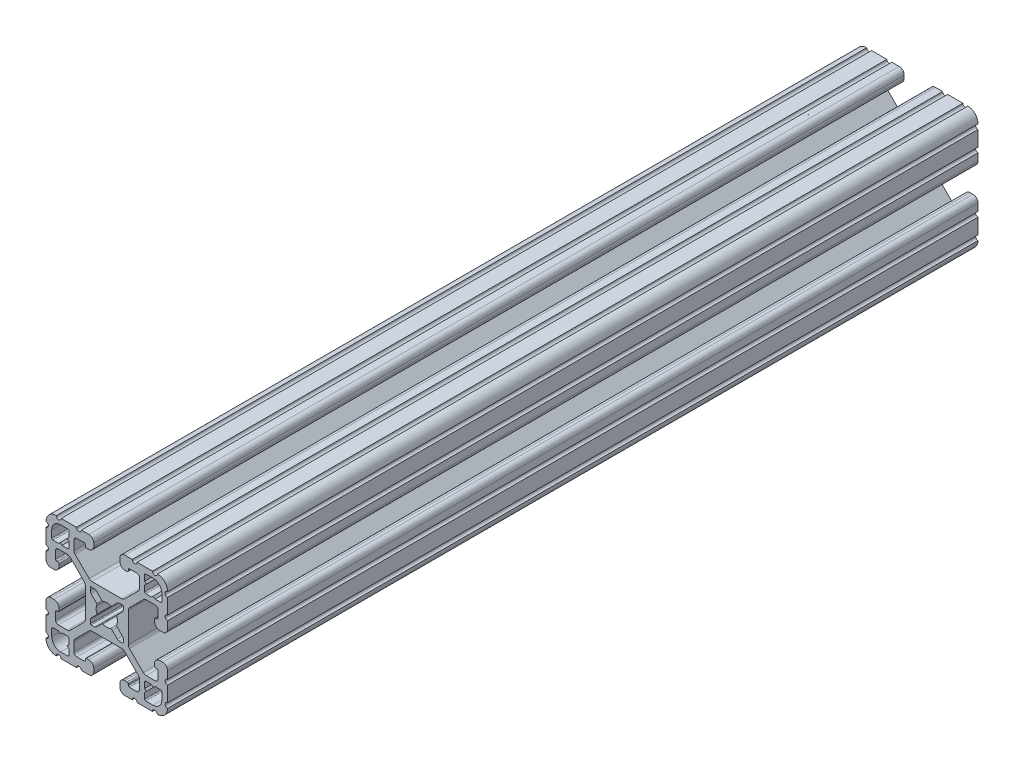
SolidWorks part; units mm, degrees
ref_plane "Front Plane" through (0, 0, 0) normal (0, 0, 1) x (1, 0, 0)
ref_plane "Top Plane" through (0, 0, 0) normal (0, 1, 0) x (1, 0, 0)
ref_plane "Right Plane" through (0, 0, 0) normal (1, 0, 0) x (0, 0, -1)
sketch "Sketch1" plane through (0, 0, 0) normal (0, 0, 1) x (1, 0, 0)
  line L0 (1.5823, 3.1988) -> (3.2921, 4.9085)
  line L1 (3.9207, 5.1689) -> (4.9149, 5.1689)
  line L2 (5.1689, 4.9149) -> (5.1689, 3.9207)
  line L3 (4.9085, 3.2921) -> (3.1988, 1.5823)
  line L4 (3.1988, -1.5823) -> (4.9085, -3.2921)
  line L5 (5.1689, -3.9207) -> (5.1689, -4.9149)
  line L6 (4.9149, -5.1689) -> (3.9207, -5.1689)
  line L7 (3.2921, -4.9085) -> (1.5823, -3.1988)
  line L8 (-1.5823, -3.1988) -> (-3.2921, -4.9085)
  line L9 (-3.9207, -5.1689) -> (-4.9149, -5.1689)
  line L10 (-5.1689, -4.9149) -> (-5.1689, -3.9207)
  line L11 (-4.9085, -3.2921) -> (-3.1988, -1.5823)
  line L12 (-3.1988, 1.5823) -> (-4.9085, 3.2921)
  line L13 (-5.1689, 3.9207) -> (-5.1689, 4.9149)
  line L14 (-4.9149, 5.1689) -> (-3.9207, 5.1689)
  line L15 (-3.2921, 4.9085) -> (-1.5823, 3.1988)
  line L16 (-11.8669, 14.0194) -> (-11.8669, 12.2479)
  line L17 (-12.2479, 11.8669) -> (-14.0195, 11.8669)
  line L18 (-14.0213, 11.8676) -> (-14.5575, 12.4039)
  line L19 (-14.5611, 12.4039) -> (-15.0973, 11.8676)
  line L20 (-15.0991, 11.8669) -> (-16.8707, 11.8669)
  line L21 (-17.2517, 12.2479) -> (-17.2517, 14.4577)
  line L22 (-14.4577, 17.2517) -> (-12.2479, 17.2517)
  line L23 (-11.8669, 16.8707) -> (-11.8669, 15.0991)
  line L24 (-11.8676, 15.0973) -> (-12.4039, 14.5611)
  line L25 (-12.4039, 14.5575) -> (-11.8676, 14.0212)
  line L26 (-14.0194, -11.8669) -> (-12.2479, -11.8669)
  line L27 (-11.8669, -12.2479) -> (-11.8669, -14.0195)
  line L28 (-11.8676, -14.0213) -> (-12.4039, -14.5575)
  line L29 (-12.4039, -14.5611) -> (-11.8676, -15.0973)
  line L30 (-11.8669, -15.0991) -> (-11.8669, -16.8707)
  line L31 (-12.2479, -17.2517) -> (-14.4577, -17.2517)
  line L32 (-17.2517, -14.4577) -> (-17.2517, -12.2479)
  line L33 (-16.8707, -11.8669) -> (-15.0991, -11.8669)
  line L34 (-15.0973, -11.8676) -> (-14.5611, -12.4039)
  line L35 (-14.5575, -12.4039) -> (-14.0212, -11.8676)
  line L36 (11.8669, -14.0194) -> (11.8669, -12.2479)
  line L37 (12.2479, -11.8669) -> (14.0195, -11.8669)
  line L38 (14.0213, -11.8676) -> (14.5575, -12.4039)
  line L39 (14.5611, -12.4039) -> (15.0973, -11.8676)
  line L40 (15.0991, -11.8669) -> (16.8707, -11.8669)
  line L41 (17.2517, -12.2479) -> (17.2517, -14.4577)
  line L42 (14.4577, -17.2517) -> (12.2479, -17.2517)
  line L43 (11.8669, -16.8707) -> (11.8669, -15.0991)
  line L44 (11.8676, -15.0973) -> (12.4039, -14.5611)
  line L45 (12.4039, -14.5575) -> (11.8676, -14.0212)
  line L46 (14.0194, 11.8669) -> (12.2479, 11.8669)
  line L47 (11.8669, 12.2479) -> (11.8669, 14.0195)
  line L48 (11.8676, 14.0213) -> (12.4039, 14.5575)
  line L49 (12.4039, 14.5611) -> (11.8676, 15.0973)
  line L50 (11.8669, 15.0991) -> (11.8669, 16.8707)
  line L51 (12.2479, 17.2517) -> (14.4577, 17.2517)
  line L52 (17.2517, 14.4577) -> (17.2517, 12.2479)
  line L53 (16.8707, 11.8669) -> (15.0991, 11.8669)
  line L54 (15.0973, 11.8676) -> (14.5611, 12.4039)
  line L55 (14.5575, 12.4039) -> (14.0212, 11.8676)
  line L56 (6.3498, -14.9848) -> (5.6531, -14.9848)
  line L57 (4.0778, -16.5601) -> (4.0778, -17.4747)
  line L58 (5.6531, -19.05) -> (7.9756, -19.05)
  line L59 (9.4996, -19.05) -> (14.2981, -19.05)
  line L60 (19.05, -14.3256) -> (19.05, -9.4996)
  line L61 (19.05, -7.9756) -> (19.05, -5.6531)
  line L62 (17.4747, -4.0778) -> (16.5601, -4.0778)
  line L63 (14.9848, -5.6531) -> (14.9848, -6.3498)
  line L64 (15.3661, -6.731) -> (15.6969, -6.731)
  line L65 (16.0782, -7.1122) -> (16.0782, -9.3968)
  line L66 (15.1881, -10.287) -> (12.3526, -10.2871)
  line L67 (11.4535, -9.9142) -> (7.1147, -5.5659)
  line L68 (6.7437, -4.6689) -> (6.7437, 4.6414)
  line L69 (7.1147, 5.5384) -> (11.481, 9.9142)
  line L70 (12.38, 10.2871) -> (15.1881, 10.287)
  line L71 (16.0782, 9.3968) -> (16.0782, 7.1122)
  line L72 (15.6969, 6.731) -> (15.3661, 6.731)
  line L73 (14.9848, 6.3498) -> (14.9848, 5.6531)
  line L74 (16.5601, 4.0778) -> (17.4747, 4.0778)
  line L75 (19.05, 5.6531) -> (19.05, 7.9756)
  line L76 (19.05, 9.4996) -> (19.05, 14.2981)
  line L77 (14.3256, 19.05) -> (9.4996, 19.05)
  line L78 (7.9756, 19.05) -> (5.6531, 19.05)
  line L79 (4.0778, 17.4747) -> (4.0778, 16.5601)
  line L80 (5.6531, 14.9848) -> (6.3498, 14.9848)
  line L81 (6.731, 15.3661) -> (6.731, 15.6969)
  line L82 (7.1122, 16.0782) -> (9.3968, 16.0782)
  line L83 (10.287, 15.1881) -> (10.2871, 12.3526)
  line L84 (9.9142, 11.4535) -> (5.5659, 7.1147)
  line L85 (4.6689, 6.7437) -> (-4.6414, 6.7437)
  line L86 (-5.5384, 7.1147) -> (-9.9142, 11.481)
  line L87 (-10.2871, 12.38) -> (-10.287, 15.1881)
  line L88 (-9.3968, 16.0782) -> (-7.1122, 16.0782)
  line L89 (-6.731, 15.6969) -> (-6.731, 15.3661)
  line L90 (-6.3498, 14.9848) -> (-5.6531, 14.9848)
  line L91 (-4.0778, 16.5601) -> (-4.0778, 17.4747)
  line L92 (-5.6531, 19.05) -> (-7.9756, 19.05)
  line L93 (-9.4996, 19.05) -> (-14.2981, 19.05)
  line L94 (-19.05, 14.3256) -> (-19.05, 9.4996)
  line L95 (-19.05, 7.9756) -> (-19.05, 5.6531)
  line L96 (-17.4747, 4.0778) -> (-16.5601, 4.0778)
  line L97 (-14.9848, 5.6531) -> (-14.9848, 6.3498)
  line L98 (-15.3661, 6.731) -> (-15.6969, 6.731)
  line L99 (-16.0782, 7.1122) -> (-16.0782, 9.3968)
  line L100 (-15.1881, 10.287) -> (-12.3526, 10.2871)
  line L101 (-11.4535, 9.9142) -> (-7.1147, 5.5659)
  line L102 (-6.7437, 4.6689) -> (-6.7437, -4.6414)
  line L103 (-7.1147, -5.5384) -> (-11.481, -9.9142)
  line L104 (-12.38, -10.2871) -> (-15.1881, -10.287)
  line L105 (-16.0782, -9.3968) -> (-16.0782, -7.1122)
  line L106 (-15.6969, -6.731) -> (-15.3661, -6.731)
  line L107 (-14.9848, -6.3498) -> (-14.9848, -5.6531)
  line L108 (-16.5601, -4.0778) -> (-17.4747, -4.0778)
  line L109 (-19.05, -5.6531) -> (-19.05, -7.9756)
  line L110 (-19.05, -9.4996) -> (-19.05, -14.2981)
  line L111 (-14.3256, -19.05) -> (-9.4996, -19.05)
  line L112 (-7.9756, -19.05) -> (-5.6531, -19.05)
  line L113 (-4.0778, -17.4747) -> (-4.0778, -16.5601)
  line L114 (-5.6531, -14.9848) -> (-6.3498, -14.9848)
  line L115 (-6.731, -15.3661) -> (-6.731, -15.6969)
  line L116 (-7.1122, -16.0782) -> (-9.3968, -16.0782)
  line L117 (-10.287, -15.1881) -> (-10.2871, -12.3526)
  line L118 (-9.9142, -11.4535) -> (-5.5659, -7.1147)
  line L119 (-4.6689, -6.7437) -> (4.6414, -6.7437)
  line L120 (5.5384, -7.1147) -> (9.9142, -11.481)
  line L121 (10.2871, -12.38) -> (10.287, -15.1881)
  line L122 (9.3968, -16.0782) -> (7.1122, -16.0782)
  line L123 (6.731, -15.6969) -> (6.731, -15.3661)
  arc A0 (1.178, 3.1119) -> (1.5823, 3.1988) centre (1.3129, 3.4682) ccw
  arc A1 (3.9207, 5.1689) -> (3.2921, 4.9085) centre (3.9207, 4.2799) ccw
  arc A2 (5.1689, 4.9149) -> (4.9149, 5.1689) centre (4.9149, 4.9149) ccw
  arc A3 (4.9085, 3.2921) -> (5.1689, 3.9207) centre (4.2799, 3.9207) ccw
  arc A4 (3.1988, 1.5823) -> (3.1119, 1.178) centre (3.4682, 1.3129) ccw
  arc A5 (3.1119, -1.178) -> (3.1119, 1.178) centre (0, 0) ccw
  arc A6 (3.1119, -1.178) -> (3.1988, -1.5823) centre (3.4682, -1.3129) ccw
  arc A7 (5.1689, -3.9207) -> (4.9085, -3.2921) centre (4.2799, -3.9207) ccw
  arc A8 (4.9149, -5.1689) -> (5.1689, -4.9149) centre (4.9149, -4.9149) ccw
  arc A9 (3.2921, -4.9085) -> (3.9207, -5.1689) centre (3.9207, -4.2799) ccw
  arc A10 (1.5823, -3.1988) -> (1.178, -3.1119) centre (1.3129, -3.4682) ccw
  arc A11 (-1.178, -3.1119) -> (1.178, -3.1119) centre (0, 0) ccw
  arc A12 (-1.178, -3.1119) -> (-1.5823, -3.1988) centre (-1.3129, -3.4682) ccw
  arc A13 (-3.9207, -5.1689) -> (-3.2921, -4.9085) centre (-3.9207, -4.2799) ccw
  arc A14 (-5.1689, -4.9149) -> (-4.9149, -5.1689) centre (-4.9149, -4.9149) ccw
  arc A15 (-4.9085, -3.2921) -> (-5.1689, -3.9207) centre (-4.2799, -3.9207) ccw
  arc A16 (-3.1988, -1.5823) -> (-3.1119, -1.178) centre (-3.4682, -1.3129) ccw
  arc A17 (-3.1119, 1.178) -> (-3.1119, -1.178) centre (0, 0) ccw
  arc A18 (-3.1119, 1.178) -> (-3.1988, 1.5823) centre (-3.4682, 1.3129) ccw
  arc A19 (-5.1689, 3.9207) -> (-4.9085, 3.2921) centre (-4.2799, 3.9207) ccw
  arc A20 (-4.9149, 5.1689) -> (-5.1689, 4.9149) centre (-4.9149, 4.9149) ccw
  arc A21 (-3.2921, 4.9085) -> (-3.9207, 5.1689) centre (-3.9207, 4.2799) ccw
  arc A22 (-1.5823, 3.1988) -> (-1.178, 3.1119) centre (-1.3129, 3.4682) ccw
  arc A23 (1.178, 3.1119) -> (-1.178, 3.1119) centre (0, 0) ccw
  arc A24 (-11.8669, 14.0194) -> (-11.8676, 14.0212) centre (-11.8694, 14.0194) ccw
  arc A25 (-12.2479, 11.8669) -> (-11.8669, 12.2479) centre (-12.2479, 12.2479) ccw
  arc A26 (-14.0213, 11.8676) -> (-14.0195, 11.8669) centre (-14.0195, 11.8694) ccw
  arc A27 (-14.5575, 12.4039) -> (-14.5611, 12.4039) centre (-14.5593, 12.4021) ccw
  arc A28 (-15.0991, 11.8669) -> (-15.0973, 11.8676) centre (-15.0991, 11.8694) ccw
  arc A29 (-17.2517, 12.2479) -> (-16.8707, 11.8669) centre (-16.8707, 12.2479) ccw
  arc A30 (-14.4577, 17.2517) -> (-17.2517, 14.4577) centre (-14.4577, 14.4577) ccw
  arc A31 (-11.8669, 16.8707) -> (-12.2479, 17.2517) centre (-12.2479, 16.8707) ccw
  arc A32 (-11.8676, 15.0973) -> (-11.8669, 15.0991) centre (-11.8694, 15.0991) ccw
  arc A33 (-12.4039, 14.5611) -> (-12.4039, 14.5575) centre (-12.4021, 14.5593) ccw
  arc A34 (-14.0194, -11.8669) -> (-14.0212, -11.8676) centre (-14.0194, -11.8694) ccw
  arc A35 (-11.8669, -12.2479) -> (-12.2479, -11.8669) centre (-12.2479, -12.2479) ccw
  arc A36 (-11.8676, -14.0213) -> (-11.8669, -14.0195) centre (-11.8694, -14.0195) ccw
  arc A37 (-12.4039, -14.5575) -> (-12.4039, -14.5611) centre (-12.4021, -14.5593) ccw
  arc A38 (-11.8669, -15.0991) -> (-11.8676, -15.0973) centre (-11.8694, -15.0991) ccw
  arc A39 (-12.2479, -17.2517) -> (-11.8669, -16.8707) centre (-12.2479, -16.8707) ccw
  arc A40 (-17.2517, -14.4577) -> (-14.4577, -17.2517) centre (-14.4577, -14.4577) ccw
  arc A41 (-16.8707, -11.8669) -> (-17.2517, -12.2479) centre (-16.8707, -12.2479) ccw
  arc A42 (-15.0973, -11.8676) -> (-15.0991, -11.8669) centre (-15.0991, -11.8694) ccw
  arc A43 (-14.5611, -12.4039) -> (-14.5575, -12.4039) centre (-14.5593, -12.4021) ccw
  arc A44 (11.8669, -14.0194) -> (11.8676, -14.0212) centre (11.8694, -14.0194) ccw
  arc A45 (12.2479, -11.8669) -> (11.8669, -12.2479) centre (12.2479, -12.2479) ccw
  arc A46 (14.0213, -11.8676) -> (14.0195, -11.8669) centre (14.0195, -11.8694) ccw
  arc A47 (14.5575, -12.4039) -> (14.5611, -12.4039) centre (14.5593, -12.4021) ccw
  arc A48 (15.0991, -11.8669) -> (15.0973, -11.8676) centre (15.0991, -11.8694) ccw
  arc A49 (17.2517, -12.2479) -> (16.8707, -11.8669) centre (16.8707, -12.2479) ccw
  arc A50 (14.4577, -17.2517) -> (17.2517, -14.4577) centre (14.4577, -14.4577) ccw
  arc A51 (11.8669, -16.8707) -> (12.2479, -17.2517) centre (12.2479, -16.8707) ccw
  arc A52 (11.8676, -15.0973) -> (11.8669, -15.0991) centre (11.8694, -15.0991) ccw
  arc A53 (12.4039, -14.5611) -> (12.4039, -14.5575) centre (12.4021, -14.5593) ccw
  arc A54 (14.0194, 11.8669) -> (14.0212, 11.8676) centre (14.0194, 11.8694) ccw
  arc A55 (11.8669, 12.2479) -> (12.2479, 11.8669) centre (12.2479, 12.2479) ccw
  arc A56 (11.8676, 14.0213) -> (11.8669, 14.0195) centre (11.8694, 14.0195) ccw
  arc A57 (12.4039, 14.5575) -> (12.4039, 14.5611) centre (12.4021, 14.5593) ccw
  arc A58 (11.8669, 15.0991) -> (11.8676, 15.0973) centre (11.8694, 15.0991) ccw
  arc A59 (12.2479, 17.2517) -> (11.8669, 16.8707) centre (12.2479, 16.8707) ccw
  arc A60 (17.2517, 14.4577) -> (14.4577, 17.2517) centre (14.4577, 14.4577) ccw
  arc A61 (16.8707, 11.8669) -> (17.2517, 12.2479) centre (16.8707, 12.2479) ccw
  arc A62 (15.0973, 11.8676) -> (15.0991, 11.8669) centre (15.0991, 11.8694) ccw
  arc A63 (14.5611, 12.4039) -> (14.5575, 12.4039) centre (14.5593, 12.4021) ccw
  arc A64 (6.731, -15.3661) -> (6.3498, -14.9848) centre (6.35, -15.3658) ccw
  arc A65 (5.6531, -14.9848) -> (4.0778, -16.5601) centre (5.6526, -16.5596) ccw
  arc A66 (4.0778, -17.4747) -> (5.6531, -19.05) centre (5.6526, -17.4752) ccw
  arc A67 (9.4996, -19.05) -> (7.9756, -19.05) centre (8.7376, -19.05) ccw
  arc A68 (15.8221, -19.0496) -> (14.2981, -19.05) centre (15.0601, -19.05) ccw
  arc A69 (15.8221, -19.0496) -> (19.0499, -15.8496) centre (15.875, -15.875) ccw
  arc A70 (19.05, -14.3256) -> (19.0499, -15.8496) centre (19.05, -15.0876) ccw
  arc A71 (19.05, -7.9756) -> (19.05, -9.4996) centre (19.05, -8.7376) ccw
  arc A72 (19.05, -5.6531) -> (17.4747, -4.0778) centre (17.4752, -5.6526) ccw
  arc A73 (16.5601, -4.0778) -> (14.9848, -5.6531) centre (16.5596, -5.6526) ccw
  arc A74 (14.9848, -6.3498) -> (15.3661, -6.731) centre (15.3658, -6.35) ccw
  arc A75 (16.0782, -7.1122) -> (15.6969, -6.731) centre (15.6972, -7.112) ccw
  arc A76 (15.1881, -10.287) -> (16.0782, -9.3968) centre (15.1892, -9.398) ccw
  arc A77 (11.4535, -9.9142) -> (12.3526, -10.2871) centre (12.3525, -9.0171) ccw
  arc A78 (6.7437, -4.6689) -> (7.1147, -5.5659) centre (8.0137, -4.6689) ccw
  arc A79 (7.1147, 5.5384) -> (6.7437, 4.6414) centre (8.0137, 4.6414) ccw
  arc A80 (12.38, 10.2871) -> (11.481, 9.9142) centre (12.38, 9.0171) ccw
  arc A81 (16.0782, 9.3968) -> (15.1881, 10.287) centre (15.1892, 9.398) ccw
  arc A82 (15.6969, 6.731) -> (16.0782, 7.1122) centre (15.6972, 7.112) ccw
  arc A83 (15.3661, 6.731) -> (14.9848, 6.3498) centre (15.3658, 6.35) ccw
  arc A84 (14.9848, 5.6531) -> (16.5601, 4.0778) centre (16.5596, 5.6526) ccw
  arc A85 (17.4747, 4.0778) -> (19.05, 5.6531) centre (17.4752, 5.6526) ccw
  arc A86 (19.05, 9.4996) -> (19.05, 7.9756) centre (19.05, 8.7376) ccw
  arc A87 (19.0496, 15.8221) -> (19.05, 14.2981) centre (19.05, 15.0601) ccw
  arc A88 (19.0496, 15.8221) -> (15.8496, 19.0499) centre (15.875, 15.875) ccw
  arc A89 (14.3256, 19.05) -> (15.8496, 19.0499) centre (15.0876, 19.05) ccw
  arc A90 (7.9756, 19.05) -> (9.4996, 19.05) centre (8.7376, 19.05) ccw
  arc A91 (5.6531, 19.05) -> (4.0778, 17.4747) centre (5.6526, 17.4752) ccw
  arc A92 (4.0778, 16.5601) -> (5.6531, 14.9848) centre (5.6526, 16.5596) ccw
  arc A93 (6.3498, 14.9848) -> (6.731, 15.3661) centre (6.35, 15.3658) ccw
  arc A94 (7.1122, 16.0782) -> (6.731, 15.6969) centre (7.112, 15.6972) ccw
  arc A95 (10.287, 15.1881) -> (9.3968, 16.0782) centre (9.398, 15.1892) ccw
  arc A96 (9.9142, 11.4535) -> (10.2871, 12.3526) centre (9.0171, 12.3525) ccw
  arc A97 (4.6689, 6.7437) -> (5.5659, 7.1147) centre (4.6689, 8.0137) ccw
  arc A98 (-5.5384, 7.1147) -> (-4.6414, 6.7437) centre (-4.6414, 8.0137) ccw
  arc A99 (-10.2871, 12.38) -> (-9.9142, 11.481) centre (-9.0171, 12.38) ccw
  arc A100 (-9.3968, 16.0782) -> (-10.287, 15.1881) centre (-9.398, 15.1892) ccw
  arc A101 (-6.731, 15.6969) -> (-7.1122, 16.0782) centre (-7.112, 15.6972) ccw
  arc A102 (-6.731, 15.3661) -> (-6.3498, 14.9848) centre (-6.35, 15.3658) ccw
  arc A103 (-5.6531, 14.9848) -> (-4.0778, 16.5601) centre (-5.6526, 16.5596) ccw
  arc A104 (-4.0778, 17.4747) -> (-5.6531, 19.05) centre (-5.6526, 17.4752) ccw
  arc A105 (-9.4996, 19.05) -> (-7.9756, 19.05) centre (-8.7376, 19.05) ccw
  arc A106 (-15.8221, 19.0496) -> (-14.2981, 19.05) centre (-15.0601, 19.05) ccw
  arc A107 (-15.8221, 19.0496) -> (-19.0499, 15.8496) centre (-15.875, 15.875) ccw
  arc A108 (-19.05, 14.3256) -> (-19.0499, 15.8496) centre (-19.05, 15.0876) ccw
  arc A109 (-19.05, 7.9756) -> (-19.05, 9.4996) centre (-19.05, 8.7376) ccw
  arc A110 (-19.05, 5.6531) -> (-17.4747, 4.0778) centre (-17.4752, 5.6526) ccw
  arc A111 (-16.5601, 4.0778) -> (-14.9848, 5.6531) centre (-16.5596, 5.6526) ccw
  arc A112 (-14.9848, 6.3498) -> (-15.3661, 6.731) centre (-15.3658, 6.35) ccw
  arc A113 (-16.0782, 7.1122) -> (-15.6969, 6.731) centre (-15.6972, 7.112) ccw
  arc A114 (-15.1881, 10.287) -> (-16.0782, 9.3968) centre (-15.1892, 9.398) ccw
  arc A115 (-11.4535, 9.9142) -> (-12.3526, 10.2871) centre (-12.3525, 9.0171) ccw
  arc A116 (-6.7437, 4.6689) -> (-7.1147, 5.5659) centre (-8.0137, 4.6689) ccw
  arc A117 (-7.1147, -5.5384) -> (-6.7437, -4.6414) centre (-8.0137, -4.6414) ccw
  arc A118 (-12.38, -10.2871) -> (-11.481, -9.9142) centre (-12.38, -9.0171) ccw
  arc A119 (-16.0782, -9.3968) -> (-15.1881, -10.287) centre (-15.1892, -9.398) ccw
  arc A120 (-15.6969, -6.731) -> (-16.0782, -7.1122) centre (-15.6972, -7.112) ccw
  arc A121 (-15.3661, -6.731) -> (-14.9848, -6.3498) centre (-15.3658, -6.35) ccw
  arc A122 (-14.9848, -5.6531) -> (-16.5601, -4.0778) centre (-16.5596, -5.6526) ccw
  arc A123 (-17.4747, -4.0778) -> (-19.05, -5.6531) centre (-17.4752, -5.6526) ccw
  arc A124 (-19.05, -9.4996) -> (-19.05, -7.9756) centre (-19.05, -8.7376) ccw
  arc A125 (-19.0496, -15.8221) -> (-19.05, -14.2981) centre (-19.05, -15.0601) ccw
  arc A126 (-19.0496, -15.8221) -> (-15.8496, -19.0499) centre (-15.875, -15.875) ccw
  arc A127 (-14.3256, -19.05) -> (-15.8496, -19.0499) centre (-15.0876, -19.05) ccw
  arc A128 (-7.9756, -19.05) -> (-9.4996, -19.05) centre (-8.7376, -19.05) ccw
  arc A129 (-5.6531, -19.05) -> (-4.0778, -17.4747) centre (-5.6526, -17.4752) ccw
  arc A130 (-4.0778, -16.5601) -> (-5.6531, -14.9848) centre (-5.6526, -16.5596) ccw
  arc A131 (-6.3498, -14.9848) -> (-6.731, -15.3661) centre (-6.35, -15.3658) ccw
  arc A132 (-7.1122, -16.0782) -> (-6.731, -15.6969) centre (-7.112, -15.6972) ccw
  arc A133 (-10.287, -15.1881) -> (-9.3968, -16.0782) centre (-9.398, -15.1892) ccw
  arc A134 (-9.9142, -11.4535) -> (-10.2871, -12.3526) centre (-9.0171, -12.3525) ccw
  arc A135 (-4.6689, -6.7437) -> (-5.5659, -7.1147) centre (-4.6689, -8.0137) ccw
  arc A136 (5.5384, -7.1147) -> (4.6414, -6.7437) centre (4.6414, -8.0137) ccw
  arc A137 (10.2871, -12.38) -> (9.9142, -11.481) centre (9.0171, -12.38) ccw
  arc A138 (9.3968, -16.0782) -> (10.287, -15.1881) centre (9.398, -15.1892) ccw
  arc A139 (6.731, -15.6969) -> (7.1122, -16.0782) centre (7.112, -15.6972) ccw
extrude "Extrude1" add sketch "Sketch1" against normal blind 254
